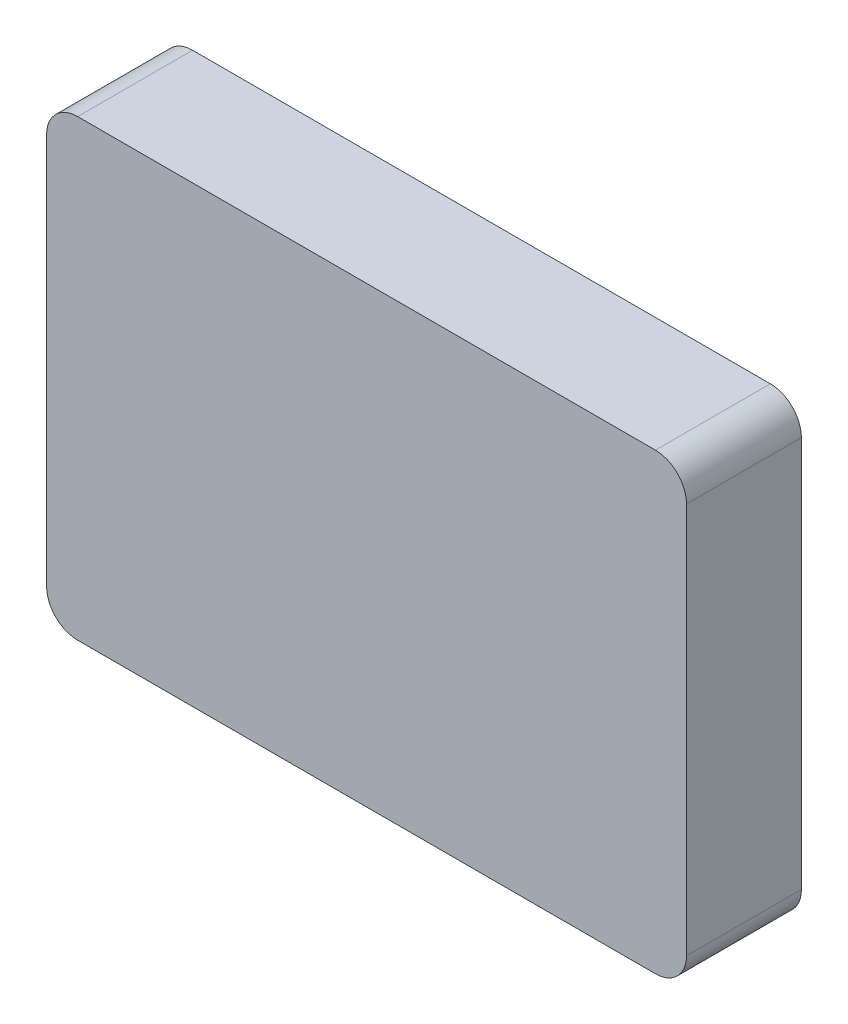
SolidWorks part; units mm, degrees
material "ABS"
ref_plane "Płaszczyzna przednia" through (0, 0, 0) normal (0, 0, 1) x (1, 0, 0)
ref_plane "Płaszczyzna górna" through (0, 0, 0) normal (0, 1, 0) x (1, 0, 0)
ref_plane "Płaszczyzna prawa" through (0, 0, 0) normal (1, 0, 0) x (0, 0, -1)
sketch "Szkic5" plane through (0, 0, 0) normal (0, 0, 1) x (1, 0, 0)
  line L0 (38, 36.5) -> (51.5, 36.5)
  line L1 (-51.5, -36.5) -> (51.5, -36.5)
  line L2 (-51.5, -36.5) -> (-51.5, 36.5)
  line L4 (51.5, -36.5) -> (51.5, 36.5)
  line L5 (-51.5, -36.5) -> (51.5, 36.5) construction
  line L6 (-51.5, 36.5) -> (51.5, -36.5) construction
  line L11 (-5.5, 36.5) -> (-51.5, 36.5)
  line L12 (-5.5, 36.5) -> (38, 36.5)
  point P0 (0, 0)
  dimension "D1" = 103
  dimension "D2" = 73
extrude "Dodanie-wyciągnięcie6" add sketch "Szkic5" against normal blind 18.5
shell "Skorupa2" thickness 2
sketch "Szkic14" plane through (0, 0, -2) normal (0, 0, -1) x (-1, 0, 0)
  line L0 (-49.5, 34.5) -> (49.5, 34.5) construction
  line L1 (-49.5, -34.5) -> (-49.5, 34.5) construction
  circle A0 centre (-40.5, 25.5) radius 5
  circle A1 centre (39.5, -24.5) radius 5
  dimension "D1" = 10
  dimension "D4" = 10
  dimension "D2" = 9
  dimension "D3" = 9
  dimension "D5" = 80
  dimension "D6" = 50
fillet "Fillet1" radius 5 4 edges at (51.5, 36.5, -9.25) (-51.5, -36.5, -9.25) (-51.5, 36.5, -9.25) (51.5, -36.5, -9.25)
